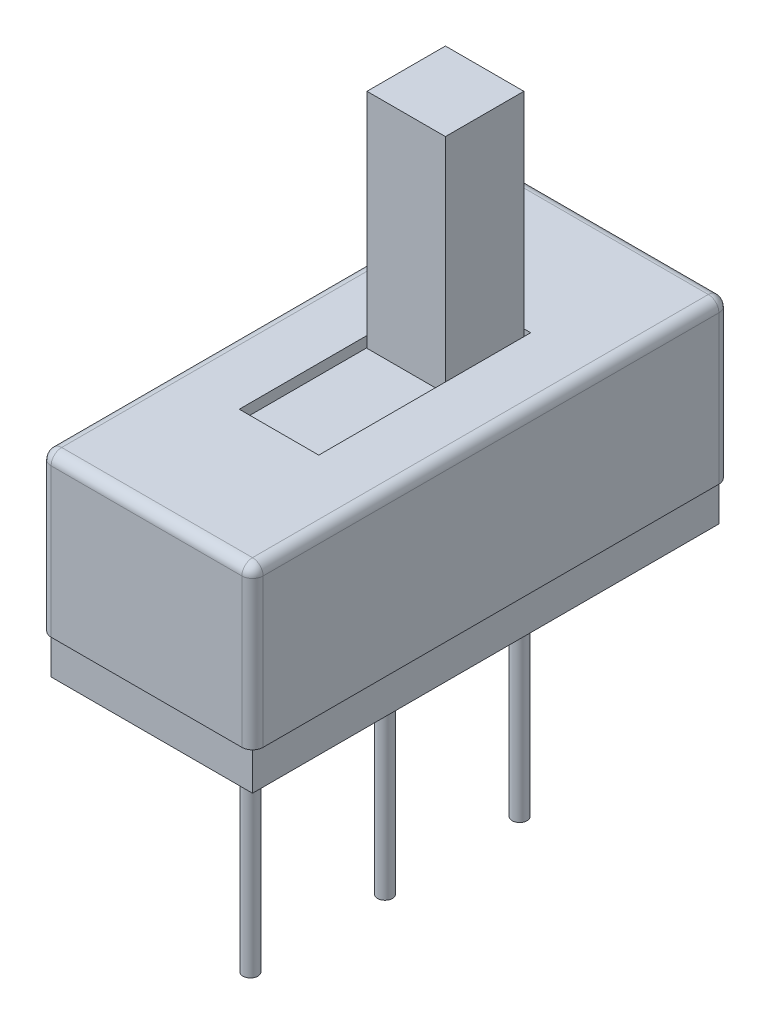
SolidWorks part; units mm, degrees
material "6061-T6 (SS)"
ref_plane "Front Plane" through (0, 0, 0) normal (0, 0, 1) x (1, 0, 0)
ref_plane "Top Plane" through (0, 0, 0) normal (0, 1, 0) x (1, 0, 0)
ref_plane "Right Plane" through (0, 0, 0) normal (1, 0, 0) x (0, 0, -1)
sketch "Sketch1" plane through (0, 0, 0) normal (0, 1, 0) x (1, 0, 0)
  line L0 (0, 4.4) -> (0, -4.4) construction
  line L1 (-1.9, 4.4) -> (1.9, 4.4)
  line L2 (-1.9, 4.4) -> (-1.9, -4.4)
  line L3 (-1.9, -4.4) -> (1.9, -4.4)
  line L4 (1.9, 4.4) -> (1.9, -4.4)
  point P6 (-2, 5.2)
  dimension "D1" = 3.8
  dimension "D2" = 8.8
extrude "Boss-Extrude1" add sketch "Sketch1" along normal blind 0.75
sketch "Sketch2" plane through (0, 0.75, 0) normal (0, 1, 0) x (1, 0, 0)
  line L0 (0, 4.5) -> (0, -4.5) construction
  line L1 (-1.8, 4.5) -> (1.8, 4.5)
  line L2 (-2, 4.3) -> (-2, -4.3)
  line L3 (-1.8, -4.5) -> (1.8, -4.5)
  line L4 (2, 4.3) -> (2, -4.3)
  arc A0 (-1.8, 4.5) -> (-2, 4.3) centre (-1.8, 4.3) ccw
  arc A1 (-2, -4.3) -> (-1.8, -4.5) centre (-1.8, -4.3) ccw
  arc A2 (1.8, -4.5) -> (2, -4.3) centre (1.8, -4.3) ccw
  arc A3 (1.8, 4.5) -> (2, 4.3) centre (1.8, 4.3) cw
  dimension "D3" = 0.2
  dimension "D1" = 4
  dimension "D2" = 9
extrude "Boss-Extrude2" add sketch "Sketch2" along normal blind 3
sketch "Sketch3" plane through (0, 3.75, 0) normal (0, 1, 0) x (1, 0, 0)
  line L0 (0, 2) -> (0, -2) construction
  line L1 (-0.75, 2) -> (0.75, 2)
  line L2 (-0.75, 2) -> (-0.75, -2)
  line L3 (-0.75, -2) -> (0.75, -2)
  line L4 (0.75, 2) -> (0.75, -2)
  dimension "D1" = 4
  dimension "D2" = 1.5
extrude "Cut-Extrude1" cut sketch "Sketch3" against normal blind 0.2
fillet "Fillet1" radius 0.2 8 edges at (1.9414, 3.75, 4.4414) (0, 3.75, 4.5) (-1.9414, 3.75, 4.4414) (-2, 3.75, 0) (-1.9414, 3.75, -4.4414) (0, 3.75, -4.5) (1.9414, 3.75, -4.4414) (2, 3.75, 0)
sketch "Sketch4" plane through (0, 3.55, 0) normal (0, 1, 0) x (1, 0, 0)
  line L0 (0, 4) -> (0, -4) construction
  line L1 (-1, 4) -> (1, 4)
  line L2 (-1, 4) -> (-1, -4)
  line L3 (-1, -4) -> (1, -4)
  line L4 (1, 4) -> (1, -4)
  dimension "D1" = 2
  dimension "D2" = 8
extrude "Cut-Extrude2" cut sketch "Sketch4" against normal blind 2
sketch "Sketch5" plane through (0, 0, 0) normal (0, -1, 0) x (1, 0, 0)
  line L0 (0, 2.54) -> (0, -2.54) construction
  circle A0 centre (0, 2.54) radius 0.14
  circle A1 centre (0, 0) radius 0.14
  circle A2 centre (0, -2.54) radius 0.14
  dimension "D2" = 0.28
  dimension "D1" = 5.08
extrude "Boss-Extrude3" add sketch "Sketch5" along normal blind 4.8
sketch "Sketch6" plane through (0, 1.55, 0) normal (0, 1, 0) x (1, 0, 0)
  line L0 (0, 4.4) -> (0, 1.88) construction
  line L2 (-0.74, 1.88) -> (0.74, 1.88)
  line L3 (-0.74, 1.88) -> (-0.74, 0.4)
  line L4 (-0.74, 0.4) -> (0.74, 0.4)
  line L5 (0.74, 1.88) -> (0.74, 0.4)
  line L6 (0, 1.88) -> (0, 0.4) construction
  line L7 (1.9, 4.4) -> (-1.9, 4.4) construction
  line L8 (0, 0.4) -> (0, -4.5) construction
  line L9 (-1.8, -4.5) -> (1.8, -4.5) construction
  point P2 (0, -4.5)
  dimension "D1" = 1.48
  dimension "D2" = 4
  dimension "D3" = 4.9
extrude "Switch ON and OFF" add sketch "Sketch6" along normal offset from surface (6.2 mm away) 7.75 separate body up to face at (0, 0, -2.4)
sketch "Sketch7" plane through (0, 1.55, 0) normal (0, 1, 0) x (1, 0, 0)
  line L4 (-1, 4) -> (-1, -4)
  line L5 (-1, -4) -> (1, -4)
  line L6 (1, -4) -> (1, 4)
  line L7 (1, 4) -> (-1, 4)
  line L8 (-1, 4) -> (-1, -4)
  line L9 (-1, -4) -> (1, -4)
  line L10 (1, -4) -> (1, 4)
  line L11 (1, 4) -> (-1, 4)
  dimension "D1" = 0
extrude "Boss-Extrude5" add sketch "Sketch7" along normal up to surface (2 mm away) up to face at (0, 3.55, 0)
